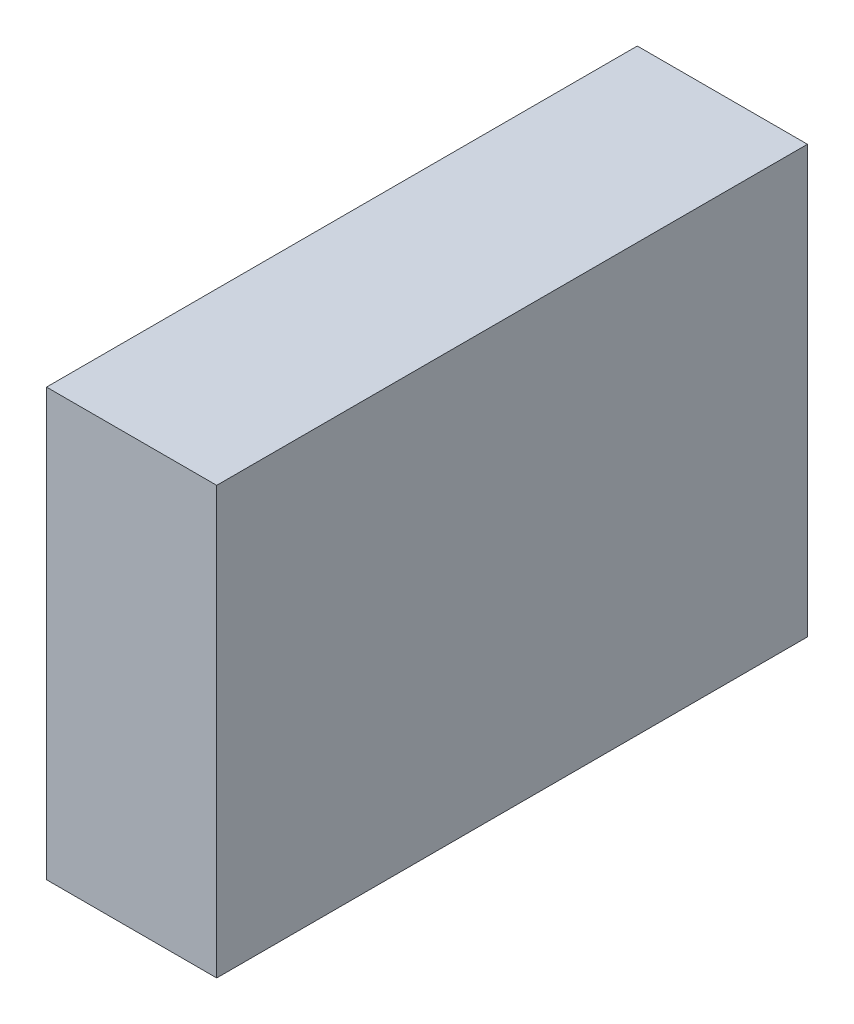
SolidWorks part; units mm, degrees
ref_plane "Front Plane" through (0, 0, 0) normal (0, 0, 1) x (1, 0, 0)
ref_plane "Top Plane" through (0, 0, 0) normal (0, 1, 0) x (1, 0, 0)
ref_plane "Right Plane" through (0, 0, 0) normal (1, 0, 0) x (0, 0, -1)
sketch "Sketch1" plane through (0, 0, 0) normal (0, 0, 1) x (1, 0, 0)
  line L1 (0, 0) -> (263.398, 0)
  line L2 (0, 0) -> (0, 660.4)
  line L3 (0, 660.4) -> (263.398, 660.4)
  line L4 (263.398, 0) -> (263.398, 660.4)
  dimension "D1" = 263.398
  dimension "D2" = 660.4
extrude "Boss-Extrude1" add sketch "Sketch1" along normal blind 914.4
